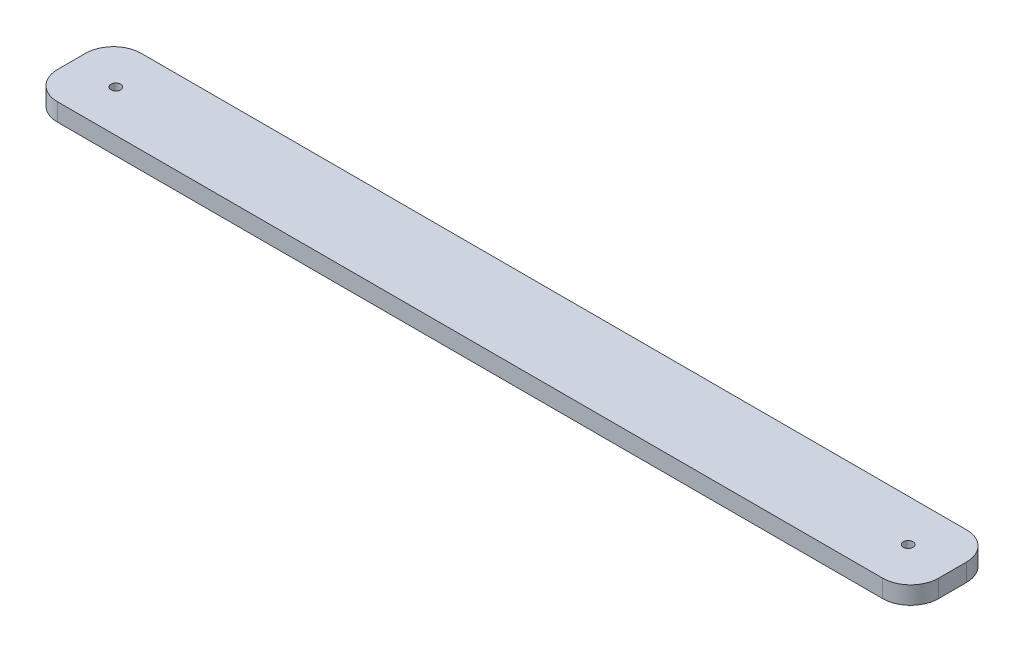
SolidWorks part; units mm, degrees
ref_plane "Front Plane" through (0, 0, 0) normal (0, 0, 1) x (1, 0, 0)
ref_plane "Top Plane" through (0, 0, 0) normal (0, 1, 0) x (1, 0, 0)
ref_plane "Right Plane" through (0, 0, 0) normal (1, 0, 0) x (0, 0, -1)
sketch "Sketch1" plane through (0, 0, 0) normal (0, 1, 0) x (1, 0, 0)
  line L1 (-157.695, 15) -> (157.695, 15)
  line L2 (-157.695, 15) -> (-157.695, -15)
  line L3 (-157.695, -15) -> (157.695, -15)
  line L4 (157.695, 15) -> (157.695, -15)
  line L5 (-157.695, 15) -> (157.695, -15) construction
  line L6 (-157.695, -15) -> (157.695, 15) construction
  point P0 (0, 0)
  dimension "D1" = 315.39
  dimension "D2" = 30
extrude "Boss-Extrude1" add sketch "Sketch1" along normal blind 6.35
sketch "Sketch4" plane through (0, 6.35, 0) normal (0, 1, 0) x (1, 0, 0)
  line L0 (-157.695, 15) -> (-157.695, -15) construction
  line L1 (157.695, 15) -> (-157.695, 15) construction
  line L3 (157.695, -15) -> (157.695, 15) construction
  circle A0 centre (-141.815, 0) radius 1.75
  circle A1 centre (141.815, 0) radius 1.75
  point P2 (-157.695, 0)
  point P11 (157.695, 0)
  dimension "D1" = 15.88
  dimension "D3" = 3.5
  dimension "D4" = 15
  dimension "D6" = 3.5
  dimension "D2" = 15
  dimension "D5" = 15.88
extrude "Cut-Extrude3" cut sketch "Sketch4" against normal through all
fillet "Fillet3" radius 10 4 edges at (157.695, 3.175, 15) (-157.695, 3.175, 15) (-157.695, 3.175, -15) (157.695, 3.175, -15)
